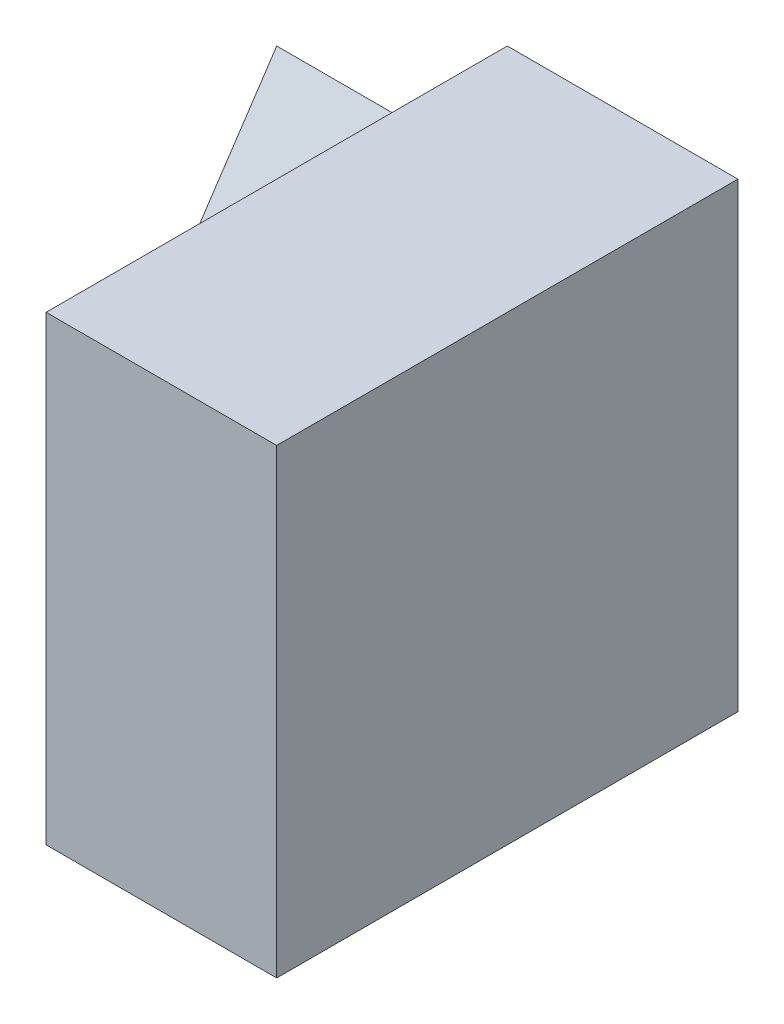
SolidWorks part; units mm, degrees
ref_plane "Front Plane" through (0, 0, 0) normal (0, 0, 1) x (1, 0, 0)
ref_plane "Top Plane" through (0, 0, 0) normal (0, 1, 0) x (1, 0, 0)
ref_plane "Right Plane" through (0, 0, 0) normal (1, 0, 0) x (0, 0, -1)
sketch "Sketch1" plane through (0, 0, 0) normal (1, 0, 0) x (0, 0, -1)
  line L1 (0, 0) -> (4, 0)
  line L2 (0, 0) -> (0, 4)
  line L3 (0, 4) -> (4, 4)
  line L4 (4, 0) -> (4, 4)
  dimension "D1" = 4
  dimension "D2" = 4
extrude "Boss-Extrude1" add sketch "Sketch1" along normal blind 2
sketch "Sketch2" plane through (0, 0, 0) normal (-1, 0, 0) x (0, 0, 1)
  line L1 (-4, 0) -> (-2, 0)
  line L2 (-4, 0) -> (-4, 3)
  line L3 (-4, 3) -> (-2, 3)
  line L4 (-2, 0) -> (-2, 3)
  dimension "D1" = 3
  dimension "D2" = 2
extrude "Boss-Extrude2" add sketch "Sketch2" along normal blind 2
sketch "Sketch3" plane through (-2, 0, 0) normal (-1, 0, 0) x (0, 0, 1)
  line L0 (-4, 3) -> (-2, 3)
  line L1 (-2, 3) -> (-2, 0)
  line L2 (-2, 0) -> (-4, 3)
extrude "Cut-Extrude1" cut sketch "Sketch3" against normal blind 2
